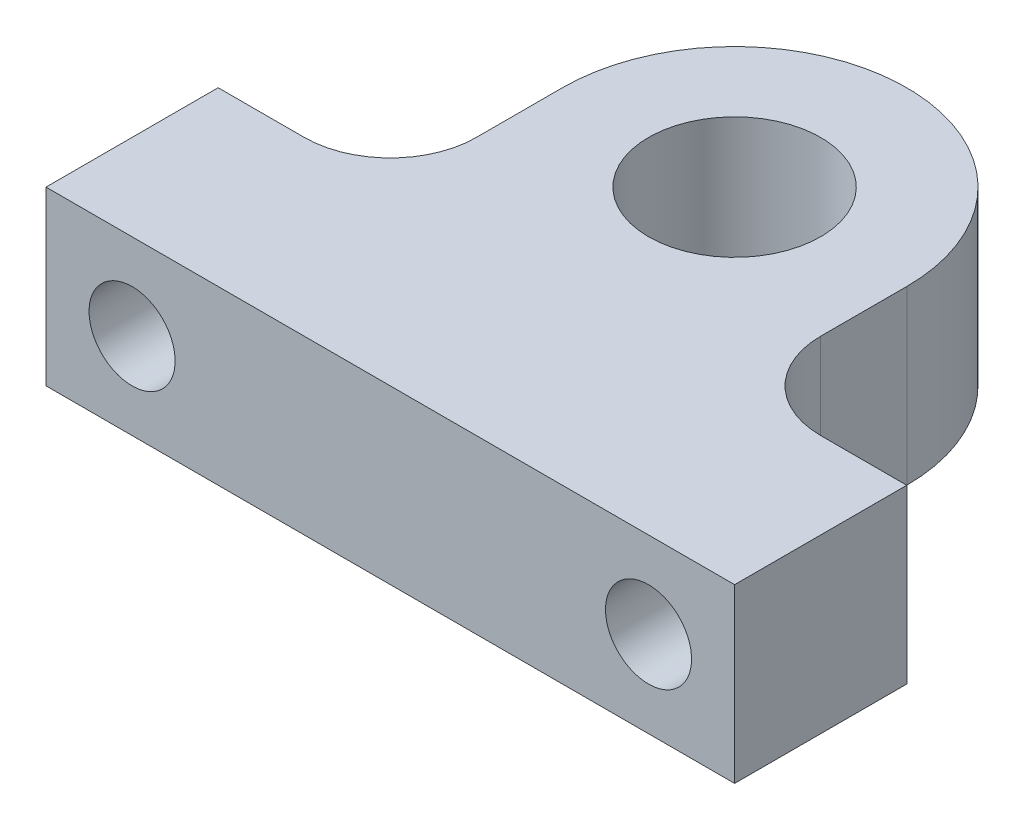
SolidWorks part; units mm, degrees
material "6061-T6 (SS)"
ref_plane "Front Plane" through (0, 0, 0) normal (0, 0, 1) x (1, 0, 0)
ref_plane "Top Plane" through (0, 0, 0) normal (0, 1, 0) x (1, 0, 0)
ref_plane "Right Plane" through (0, 0, 0) normal (1, 0, 0) x (0, 0, -1)
sketch "Sketch1" plane through (0, 0, 0) normal (0, 1, 0) x (1, 0, 0)
  line L0 (-12.7, 0) -> (-12.7, -12.7)
  line L1 (-12.7, -12.7) -> (-25.4, -12.7)
  line L2 (-25.4, -12.7) -> (-25.4, -25.4)
  line L3 (-25.4, -25.4) -> (25.4, -25.4)
  line L4 (25.4, -25.4) -> (25.4, -12.7)
  line L5 (12.7, 0) -> (12.7, -12.7)
  line L6 (12.7, -12.7) -> (25.4, -12.7)
  circle A0 centre (0, 0) radius 6.35
  arc A1 (12.7, 0) -> (-12.7, 0) centre (0, 0) ccw
  dimension "D1" = 12.7
  dimension "D2" = 25.4
  dimension "D3" = 12.7
  dimension "D4" = 12.7
extrude "Boss-Extrude1" add sketch "Sketch1" along normal blind 12.7
fillet "Fillet1" radius 6.35 2 edges at (-12.7, 6.35, 12.7) (12.7, 6.35, 12.7)
sketch "Sketch2" plane through (0, 0, 12.7) normal (0, 0, -1) x (-1, 0, 0)
  line L0 (25.4, 12.7) -> (25.4, 0) construction
  line L2 (19.05, 0) -> (25.4, 0) construction
  line L3 (-25.4, 12.7) -> (-25.4, 0) construction
  circle A0 centre (19.05, 6.35) radius 3.175
  circle A1 centre (-19.05, 6.35) radius 3.175
  dimension "D1" = 6.35
  dimension "D2" = 6.35
  dimension "D3" = 6.35
  dimension "D4" = 6.35
extrude "Cut-Extrude1" cut sketch "Sketch2" against normal through all both and the other way through all
